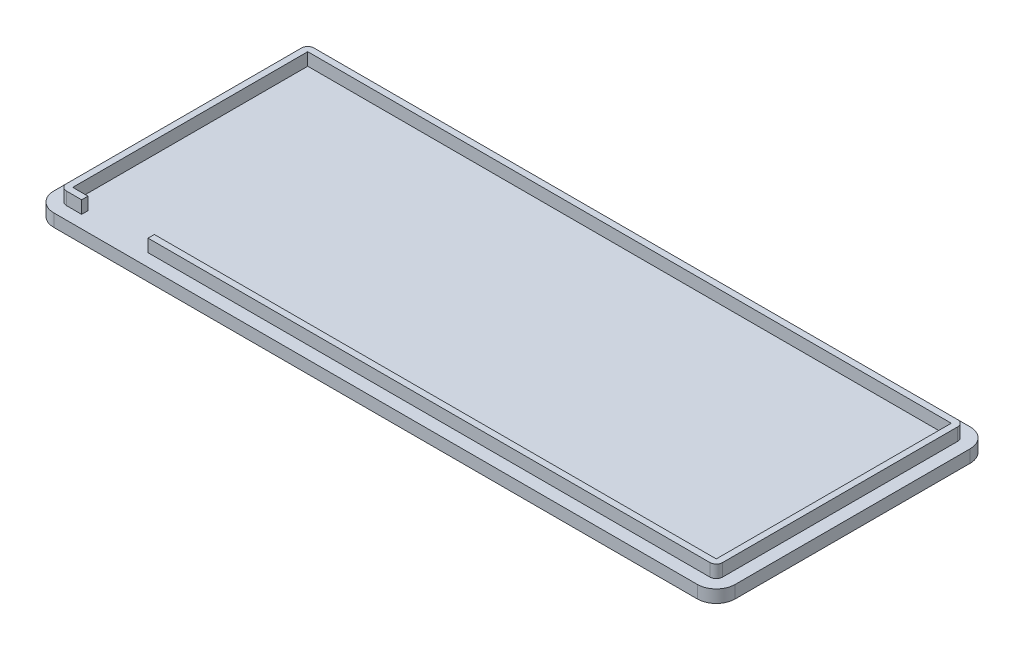
SolidWorks part; units mm, degrees
ref_plane "Front Plane" through (0, 0, 0) normal (0, 0, 1) x (1, 0, 0)
ref_plane "Top Plane" through (0, 0, 0) normal (0, 1, 0) x (1, 0, 0)
ref_plane "Right Plane" through (0, 0, 0) normal (1, 0, 0) x (0, 0, -1)
sketch "Sketch1" plane through (0, 0, 0) normal (0, 1, 0) x (1, 0, 0)
  line L1 (51, -21.625) -> (-51, -21.625)
  line L2 (54, -18.625) -> (54, 18.625)
  line L3 (51, 21.625) -> (-51, 21.625)
  line L4 (-54, -18.625) -> (-54, 18.625)
  line L5 (54, -21.625) -> (-54, 21.625) construction
  line L6 (54, 21.625) -> (-54, -21.625) construction
  arc A0 (-51, -21.625) -> (-54, -18.625) centre (-51, -18.625) cw
  arc A1 (51, -21.625) -> (54, -18.625) centre (51, -18.625) ccw
  arc A2 (54, 18.625) -> (51, 21.625) centre (51, 18.625) ccw
  arc A3 (-51, 21.625) -> (-54, 18.625) centre (-51, 18.625) ccw
  point P0 (0, 0)
  dimension "D3" = 3
  dimension "D1" = 108
  dimension "D2" = 43.25
extrude "Boss-Extrude1" add sketch "Sketch1" along normal blind 2
sketch "Sketch2" plane through (0, 2, 0) normal (0, 1, 0) x (1, 0, 0)
  line L1 (51, -19.625) -> (-51, -19.625)
  line L2 (52, -18.625) -> (52, 18.625)
  line L3 (51, 19.625) -> (-51, 19.625)
  line L4 (-52, -18.625) -> (-52, 18.625)
  line L5 (52, -19.625) -> (-52, 19.625) construction
  line L6 (52, 19.625) -> (-52, -19.625) construction
  line L7 (51, -18.625) -> (-51, -18.625)
  line L8 (51, -18.625) -> (51, 18.625)
  line L9 (51, 18.625) -> (-51, 18.625)
  line L10 (-51, -18.625) -> (-51, 18.625)
  line L11 (51, -18.625) -> (-51, 18.625) construction
  line L12 (51, 18.625) -> (-51, -18.625) construction
  arc A0 (-51, -19.625) -> (-52, -18.625) centre (-51, -18.625) cw
  arc A1 (51, -19.625) -> (52, -18.625) centre (51, -18.625) ccw
  arc A2 (52, 18.625) -> (51, 19.625) centre (51, 18.625) ccw
  arc A3 (-51, 19.625) -> (-52, 18.625) centre (-51, 18.625) ccw
  point P0 (0, 0)
  point P18 (0, 0)
  dimension "D3" = 1
  dimension "D1" = 104
  dimension "D2" = 39.25
extrude "Boss-Extrude2" add sketch "Sketch2" along normal blind 2
sketch "Sketch3" plane through (0, 0, 19.625) normal (0, 0, 1) x (1, 0, 0)
  line L0 (-54, 2) -> (-48.5847, 2) construction
  line L2 (-51, 2) -> (51, 2) construction
  line L3 (-48.5847, 2) -> (-38.0582, 2) construction
  line L4 (-51, 2) -> (51, 2) construction
  line L6 (-48.5847, 2) -> (-38.0582, 2)
  line L7 (-48.5847, 2) -> (-48.5847, 5.9072)
  line L8 (-48.5847, 5.9072) -> (-38.0582, 5.9072)
  line L9 (-38.0582, 2) -> (-38.0582, 5.9072)
extrude "Cut-Extrude1" cut sketch "Sketch3" against normal blind 2
